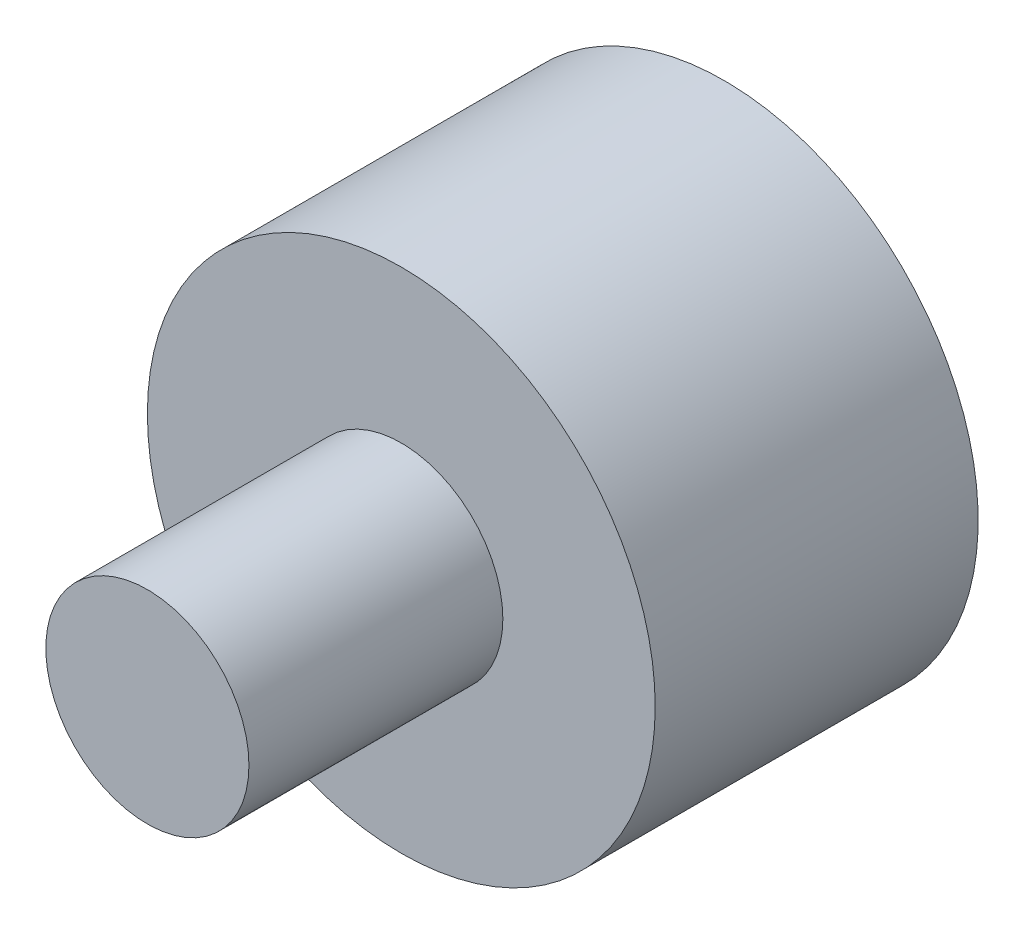
SolidWorks part; units mm, degrees
ref_plane "Front Plane" through (0, 0, 0) normal (0, 0, 1) x (1, 0, 0)
ref_plane "Top Plane" through (0, 0, 0) normal (0, 1, 0) x (1, 0, 0)
ref_plane "Right Plane" through (0, 0, 0) normal (1, 0, 0) x (0, 0, -1)
sketch "Sketch1" plane through (0, 0, 0) normal (0, 0, 1) x (1, 0, 0)
  circle A0 centre (0, 0) radius 5
extrude "Boss-Extrude1" add sketch "Sketch1" along normal blind 3.36
sketch "Sketch2" plane through (0, 0, 3.36) normal (0, 0, 1) x (1, 0, 0)
  circle A0 centre (0, 0) radius 2
extrude "Boss-Extrude2" add sketch "Sketch2" along normal blind 5
sketch "Sketch3" plane through (0, 0, 0) normal (0, 0, -1) x (-1, 0, 0)
  circle A0 centre (0, 0) radius 5
extrude "Boss-Extrude3" add sketch "Sketch3" along normal blind 3
